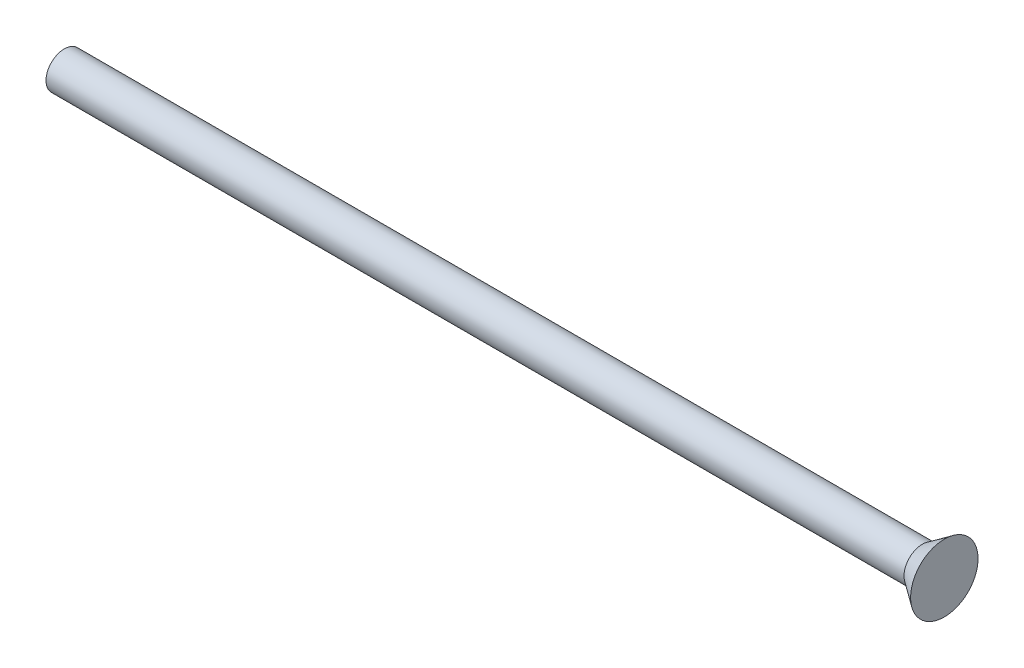
SolidWorks part; units mm, degrees
material "1060 合金"
ref_plane "前视基准面" through (0, 0, 0) normal (0, 0, 1) x (1, 0, 0)
ref_plane "上视基准面" through (0, 0, 0) normal (0, 1, 0) x (1, 0, 0)
ref_plane "右视基准面" through (0, 0, 0) normal (1, 0, 0) x (0, 0, -1)
sketch "草图1" plane through (0, 0, 0) normal (0, 0, 1) x (1, 0, 0)
  line L0 (-53.8441, 0) -> (16.0999, 0) construction
  line L1 (-50, 0) -> (-50, 1.25)
  line L2 (-50, 1.25) -> (8.5, 1.25)
  line L3 (8.5, 1.25) -> (10, 2.3)
  line L4 (-50, 0) -> (10, 0)
  line L5 (10, 2.3) -> (10, 0)
  dimension "D1" = 2.5
  dimension "D2" = 60
  dimension "D3" = 1.5
  dimension "D4" = 4.6
  dimension "D5" = 10
revolve "旋转1" add sketch "草图1" angle 360 about L0
cosmetic thread "装饰螺纹线1" parameters "D2"=2.013
